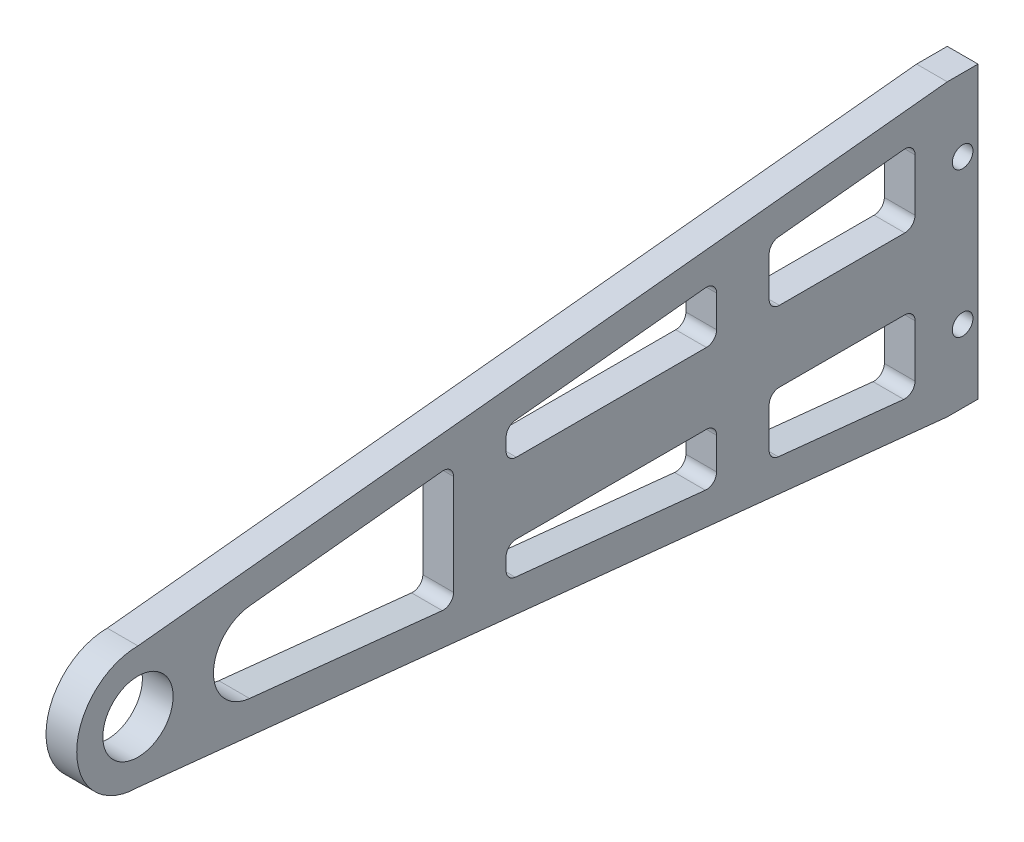
SolidWorks part; units mm, degrees
material "6061-T6 (SS)"
ref_plane "Front Plane" through (0, 0, 0) normal (0, 0, 1) x (1, 0, 0)
ref_plane "Top Plane" through (0, 0, 0) normal (0, 1, 0) x (1, 0, 0)
ref_plane "Right Plane" through (0, 0, 0) normal (1, 0, 0) x (0, 0, -1)
sketch "Sketch1" plane through (0, 0, 0) normal (1, 0, 0) x (0, 0, -1)
  line L0 (0, 0) -> (0, 35.2066) construction
  line L1 (0, 0) -> (24.8948, 24.8948) construction
  line L2 (0, 0) -> (-35.2066, 0) construction
  line L3 (0, 0) -> (-24.8948, 24.8948) construction
  line L4 (0, 0) -> (0, -35.2066) construction
  line L5 (0, 0) -> (-24.8948, -24.8948) construction
  line L6 (0, 0) -> (24.8948, -24.8948) construction
  line L7 (0, 0) -> (130.263, 0) construction
  line L8 (0, 9.5) -> (125.5, 22.5)
  line L9 (-24.8948, 5.5) -> (158.9052, 5.5) construction
  line L10 (0, -9.5) -> (125.5, -22.5)
  line L11 (125.5, 22.5) -> (130.263, 22.5)
  line L12 (130.263, 22.5) -> (130.263, -22.5)
  line L13 (130.263, -22.5) -> (125.5, -22.5)
  line L14 (-24.8948, -5.5) -> (158.9052, -5.5) construction
  line L15 (9.9121, 5.5) -> (142.9144, 19.2771) construction
  line L16 (9.9121, -5.5) -> (146.9232, -19.6924) construction
  line L17 (17.302, 6.2153) -> (47.184, 9.358)
  line L18 (48.9375, 7.7793) -> (48.9375, -7.7793)
  line L19 (47.184, -9.3581) -> (17.302, -6.2154)
  line L20 (120.5, 15.1949) -> (120.5, 7.0875)
  line L24 (120.5, -15.1949) -> (120.5, -7.0875)
  line L25 (118.7489, 16.7739) -> (99.2989, 14.7592)
  line L26 (97.875, 13.1801) -> (97.875, 7.0875)
  line L27 (99.4625, 5.5) -> (118.9125, 5.5)
  line L28 (118.9125, -5.5) -> (99.4625, -5.5)
  line L29 (97.875, -7.0875) -> (97.875, -13.1801)
  line L30 (99.2989, -14.7592) -> (118.7489, -16.7739)
  line L31 (89.7308, 7.0875) -> (89.7308, 12.0076)
  line L32 (87.9797, 13.5867) -> (58.5057, 10.5336)
  line L33 (57.0817, 8.9545) -> (57.0817, 7.0875)
  line L34 (58.6693, 5.5) -> (88.1433, 5.5)
  line L35 (89.7308, -7.0875) -> (89.7308, -12.0076)
  line L36 (87.9797, -13.5867) -> (58.5057, -10.5336)
  line L37 (57.0817, -8.9545) -> (57.0817, -7.0875)
  line L38 (58.6693, -5.5) -> (88.1433, -5.5)
  circle A0 centre (0, 0) radius 5.4494
  arc A1 (0, 9.5) -> (0, -9.5) centre (0, 0) ccw
  arc A2 (48.9375, -7.7793) -> (47.184, -9.3581) centre (47.35, -7.7793) cw
  arc A3 (99.2989, -14.7592) -> (97.875, -13.1801) centre (99.4625, -13.1801) cw
  arc A4 (118.7489, -16.7739) -> (120.5, -15.1949) centre (118.9125, -15.1949) ccw
  arc A5 (120.5, -7.0875) -> (118.9125, -5.5) centre (118.9125, -7.0875) ccw
  arc A6 (97.875, -7.0875) -> (99.4625, -5.5) centre (99.4625, -7.0875) cw
  arc A7 (89.7308, -12.0076) -> (87.9797, -13.5867) centre (88.1433, -12.0076) cw
  arc A8 (89.7308, -7.0875) -> (88.1433, -5.5) centre (88.1433, -7.0875) ccw
  arc A9 (57.0817, -8.9545) -> (58.5057, -10.5336) centre (58.6692, -8.9545) ccw
  arc A10 (57.0817, -7.0875) -> (58.6693, -5.5) centre (58.6692, -7.0875) cw
  arc A11 (48.9375, 7.7793) -> (47.184, 9.358) centre (47.35, 7.7793) ccw
  arc A14 (99.4625, 5.5) -> (97.875, 7.0875) centre (99.4625, 7.0875) cw
  arc A15 (118.9125, 5.5) -> (120.5, 7.0875) centre (118.9125, 7.0875) ccw
  arc A16 (120.5, 15.1949) -> (118.7489, 16.7739) centre (118.9125, 15.1949) ccw
  arc A17 (97.875, 13.1801) -> (99.2989, 14.7592) centre (99.4625, 13.1801) cw
  arc A18 (88.1433, 5.5) -> (89.7308, 7.0875) centre (88.1433, 7.0875) ccw
  arc A19 (89.7308, 12.0076) -> (87.9797, 13.5867) centre (88.1433, 12.0076) ccw
  arc A20 (57.0817, 7.0875) -> (58.6693, 5.5) centre (58.6692, 7.0875) ccw
  arc A21 (57.0817, 8.9545) -> (58.5057, 10.5336) centre (58.6692, 8.9545) cw
  arc A25 (17.302, -6.2154) -> (17.302, 6.2153) centre (17.9593, 0) cw
  point P11 (0, 9.5)
  point P12 (-9.5, 0)
  point P13 (0, -9.5)
  point P17 (0, 5.5)
  point P22 (0, -5.5)
  point P31 (9.9121, 5.5)
  point P32 (48.9375, 9.5425)
  point P35 (9.9121, -5.5)
  point P36 (120.5, 16.9553)
  point P39 (65.1315, 0)
  point P40 (32.625, 0)
  point P41 (97.875, 0)
  point P42 (120.5, -16.9553)
  point P45 (48.9375, -9.5425)
  point P51 (81.5625, 0)
  point P52 (114.1875, 0)
  point P53 (48.9375, 9.5425)
  point P54 (57.0817, 0)
  point P59 (73.4183, 0)
  point P60 (89.7308, 0)
  point P67 (127.8815, 22.5)
  point P70 (127.8815, -22.5)
  point P72 (97.875, -14.6117)
  point P75 (120.5, -16.9553)
  point P78 (120.5, -5.5)
  point P81 (97.875, -5.5)
  point P84 (89.7308, -13.7681)
  point P87 (89.7308, -5.5)
  point P90 (57.0817, -10.3861)
  point P93 (57.0817, -5.5)
  point P96 (48.9375, -9.5425)
  point P105 (97.875, 5.5)
  point P108 (120.5, 5.5)
  point P111 (120.5, 16.9553)
  point P114 (97.875, 14.6117)
  point P117 (89.7308, 5.5)
  point P120 (89.7308, 13.7681)
  point P123 (57.0817, 5.5)
  point P126 (57.0817, 10.3861)
  point P132 (48.9375, 9.5425)
  dimension "D1" = 1.5875
  dimension "D2" = 1.5875
  dimension "D3" = 4.763
  dimension "D4" = 130.263
  dimension "D5" = 139.763
  dimension "D6" = 45
extrude "Boss-Extrude1" add sketch "Sketch1" along normal mid plane 4.763
hole_wizard "M3 Clearance Hole1" positions "Sketch4" profile "Sketch3" hole size "M3" standard "ANSI Metric" end condition through all
sketch "Sketch4" plane through (2.3815, 0, 0) normal (1, 0, 0) x (0, 0, -1)
  line L3 (127.8815, 22.5) -> (127.8815, -22.5) construction
  line L4 (130.263, 22.5) -> (125.5, 22.5) construction
  line L5 (125.5, -22.5) -> (130.263, -22.5) construction
  point P0 (127.8815, 11.25)
  point P2 (127.8815, -11.25)
  dimension "D1" = 11.25
  dimension "D2" = 11.25
sketch "Sketch3" plane through (2.3815, 11.25, -127.8815) normal (0, 1, 0) x (0, 0, -1)
  line L0 (0, 0) -> (0, 4.763)
  line L1 (0, 4.763) -> (1.6, 4.763)
  line L2 (1.6, 4.763) -> (1.6, 0)
  line L5 (1.6, 0) -> (0, 0)
  line L11 (0, -6.35) -> (0, 107.95) construction
  dimension "Thru Hole Dia." = 3.2
  dimension "Thru Hole Depth" = 4.763
